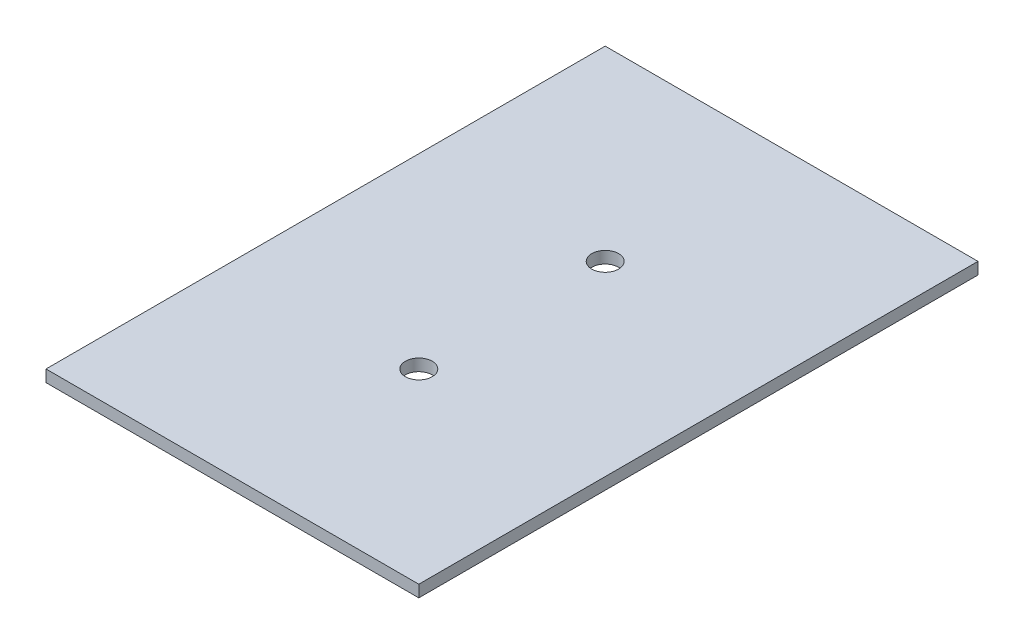
SolidWorks part; units mm, degrees
ref_plane "Front Plane" through (0, 0, 0) normal (0, 0, 1) x (1, 0, 0)
ref_plane "Top Plane" through (0, 0, 0) normal (0, 1, 0) x (1, 0, 0)
ref_plane "Right Plane" through (0, 0, 0) normal (1, 0, 0) x (0, 0, -1)
sketch "Sketch1" plane through (0, 0, 0) normal (0, 1, 0) x (1, 0, 0)
  line L1 (-22, -33) -> (22, -33)
  line L2 (-22, -33) -> (-22, 33)
  line L3 (-22, 33) -> (22, 33)
  line L4 (22, -33) -> (22, 33)
  line L5 (-22, -33) -> (22, 33) construction
  line L6 (-22, 33) -> (22, -33) construction
  point P0 (0, 0)
  dimension "D1" = 66
  dimension "D2" = 44
extrude "Boss-Extrude1" add sketch "Sketch1" along normal blind 1.4
sketch "Sketch2" plane through (0, 1.4, 0) normal (0, 1, 0) x (1, 0, 0)
  line L0 (0, 33) -> (0, -33) construction
  line L1 (22, 33) -> (-22, 33) construction
  line L2 (-22, -33) -> (22, -33) construction
  circle A0 centre (0, 11) radius 1.585
  circle A1 centre (0, -11) radius 1.585
  dimension "D1" = 3.17
  dimension "D2" = 3.17
  dimension "D3" = 11
  dimension "D4" = 11
extrude "Cut-Extrude1" cut sketch "Sketch2" against normal through all
